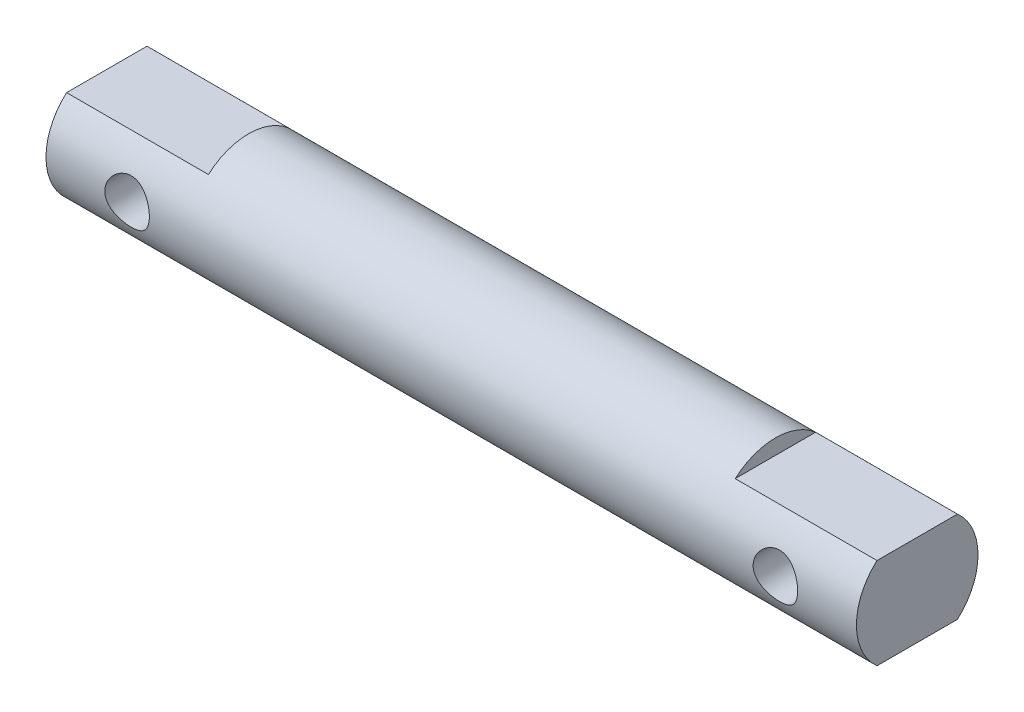
SolidWorks part; units mm, degrees
material "Plain Carbon Steel"
ref_plane "Front Plane" through (0, 0, 0) normal (0, 0, 1) x (1, 0, 0)
ref_plane "Top Plane" through (0, 0, 0) normal (0, 1, 0) x (1, 0, 0)
ref_plane "Right Plane" through (0, 0, 0) normal (1, 0, 0) x (0, 0, -1)
sketch "Sketch1" plane through (0, 0, 0) normal (0, 0, 1) x (1, 0, 0)
  line L0 (0, 0) -> (45.9529, 0) construction
  line L1 (-20, 3) -> (20, 3)
  line L2 (-20, 3) -> (-20, 0)
  line L3 (-20, 0) -> (20, 0)
  line L4 (20, 3) -> (20, 0)
  line L5 (0, 0) -> (0, 22.8572) construction
  line L6 (-13, 3) -> (-13, 0) construction
  line L7 (13, 3) -> (13, 0) construction
  dimension "D1" = 6
  dimension "D2" = 26
  dimension "D3" = 7
revolve "Revolve1" add sketch "Sketch1" angle 360 about L0
sketch "Sketch2" plane through (0, 0, 0) normal (0, 0, 1) x (1, 0, 0)
  line L0 (0, 0) -> (-31.5706, 0) construction
  line L1 (-20, 3) -> (-13, 3)
  line L2 (-20, 3) -> (-20, 2.25)
  line L3 (-20, 2.25) -> (-13, 2.25)
  line L4 (-13, 3) -> (-13, 2.25)
  line L5 (-20, -2.25) -> (-13, -2.25)
  line L6 (-20, -2.25) -> (-20, -3)
  line L7 (-20, -3) -> (-13, -3)
  line L8 (-13, -2.25) -> (-13, -3)
  line L9 (13, 3) -> (20, 3)
  line L10 (13, 3) -> (13, 2.25)
  line L11 (13, 2.25) -> (20, 2.25)
  line L12 (20, 3) -> (20, 2.25)
  line L13 (20, -2.25) -> (13, -2.25)
  line L14 (20, -2.25) -> (20, -3)
  line L15 (20, -3) -> (13, -3)
  line L16 (13, -2.25) -> (13, -3)
  line L17 (-20, 3) -> (-20, -3) construction
  line L18 (20, -3) -> (20, 3) construction
  line L19 (20, 3) -> (-20, 3) construction
  line L20 (-20, -3) -> (20, -3) construction
  dimension "D1" = 4.5
  dimension "D2" = 7
extrude "Cut-Extrude1" cut sketch "Sketch2" against normal through all and the other way through all
sketch "Sketch3" plane through (0, 0, 0) normal (0, 0, 1) x (1, 0, 0)
  line L0 (16, 0) -> (20, 0) construction
  line L1 (20, -2.25) -> (20, 2.25) construction
  line L2 (-16, 0) -> (-20, 0) construction
  line L3 (-20, 2.25) -> (-20, -2.25) construction
  circle A0 centre (-16, 0) radius 1.1
  circle A1 centre (16, 0) radius 1.1
  dimension "D1" = 2.2
  dimension "D2" = 4
extrude "Cut-Extrude2" cut sketch "Sketch3" against normal through all and the other way through all
